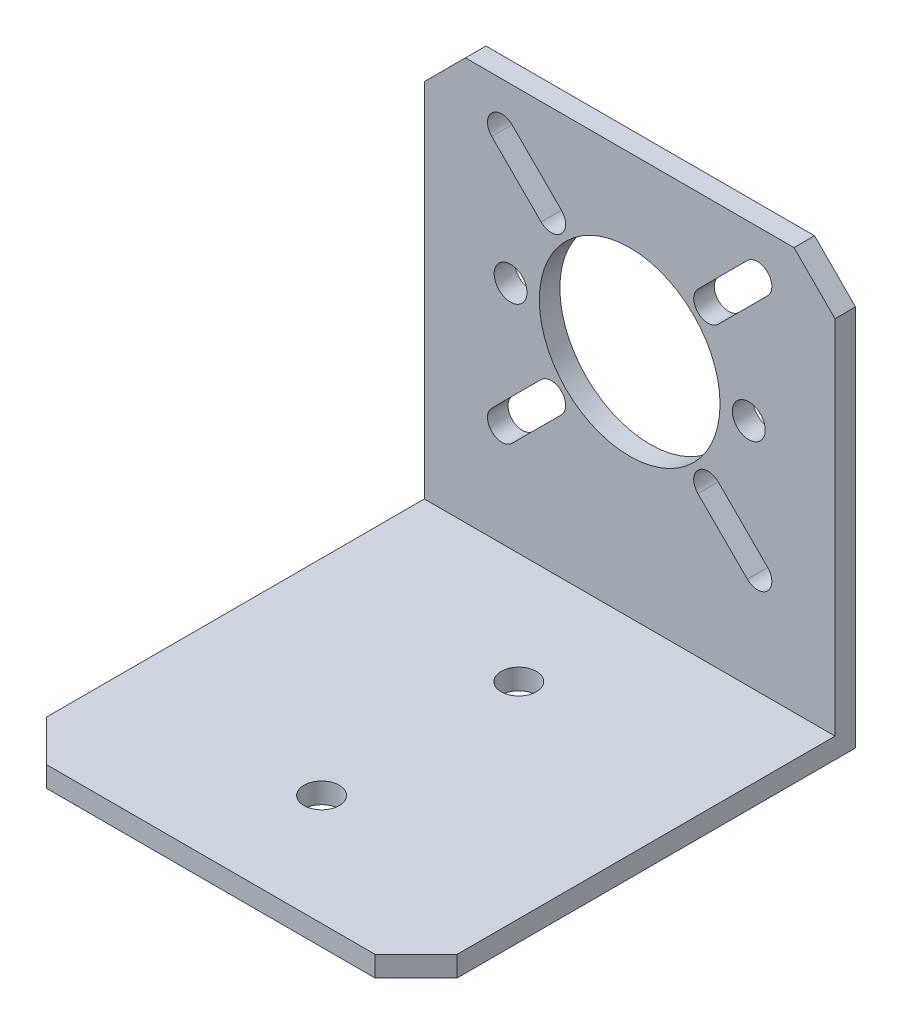
SolidWorks part; units mm, degrees
ref_plane "前视基准面" through (0, 0, 0) normal (0, 0, 1) x (1, 0, 0)
ref_plane "上视基准面" through (0, 0, 0) normal (0, 1, 0) x (1, 0, 0)
ref_plane "右视基准面" through (0, 0, 0) normal (1, 0, 0) x (0, 0, -1)
sketch "草图1" plane through (0, 0, 0) normal (0, 1, 0) x (1, 0, 0)
  line L1 (-25, 1.25) -> (25, 1.25)
  line L2 (-25, 1.25) -> (-25, -1.25)
  line L3 (-25, -1.25) -> (25, -1.25)
  line L4 (25, 1.25) -> (25, -1.25)
  line L5 (-25, 1.25) -> (25, -1.25) construction
  line L6 (-25, -1.25) -> (25, 1.25) construction
  point P1 (0, 0)
  dimension "D1" = 50
  dimension "D2" = 2.5
sketch "草图14" plane through (0, 0, 0) normal (0, 0, 1) x (1, 0, 0)
  line L0 (0, 25.75) -> (0, -25.75) construction
  line L1 (-25, 25.75) -> (25, 25.75)
  line L2 (-25, 25.75) -> (-25, -25.75)
  line L3 (-25, -25.75) -> (25, -25.75)
  line L4 (25, 25.75) -> (25, -25.75)
  line L5 (-25, 25.75) -> (25, -25.75) construction
  line L6 (-25, -25.75) -> (25, 25.75) construction
  line L7 (-22, 4.75) -> (22, 4.75) construction
  line L8 (0, 4.75) -> (-21.3712, 26.1212) construction
  line L9 (-15.5563, 20.3063) -> (-9.5459, 14.2959) construction
  line L10 (-14.3189, 21.5438) -> (-8.3085, 15.5334)
  line L11 (-16.7938, 19.0689) -> (-10.7834, 13.0585)
  line L12 (15.5563, 20.3063) -> (9.5459, 14.2959) construction
  line L13 (14.3189, 21.5438) -> (8.3085, 15.5334)
  line L14 (16.7938, 19.0689) -> (10.7834, 13.0585)
  line L15 (-15.5563, -10.8063) -> (-9.5459, -4.7959) construction
  line L16 (-14.3189, -12.0438) -> (-8.3085, -6.0334)
  line L17 (-16.7938, -9.5689) -> (-10.7834, -3.5585)
  line L18 (15.5563, -10.8063) -> (9.5459, -4.7959) construction
  line L19 (14.3189, -12.0438) -> (8.3085, -6.0334)
  line L20 (16.7938, -9.5689) -> (10.7834, -3.5585)
  circle A0 centre (0, 4.75) radius 11
  circle A1 centre (0, 4.75) radius 13.5 construction
  circle A2 centre (0, 4.75) radius 22 construction
  circle A3 centre (-14.5, 4.75) radius 2
  circle A4 centre (14.5, 4.75) radius 2
  arc A5 (-14.3189, 21.5438) -> (-16.7938, 19.0689) centre (-15.5563, 20.3063) ccw
  arc A6 (-10.7834, 13.0585) -> (-8.3085, 15.5334) centre (-9.5459, 14.2959) ccw
  arc A7 (14.3189, 21.5438) -> (16.7938, 19.0689) centre (15.5563, 20.3063) cw
  arc A8 (10.7834, 13.0585) -> (8.3085, 15.5334) centre (9.5459, 14.2959) cw
  arc A9 (-14.3189, -12.0438) -> (-16.7938, -9.5689) centre (-15.5563, -10.8063) cw
  arc A10 (-10.7834, -3.5585) -> (-8.3085, -6.0334) centre (-9.5459, -4.7959) cw
  arc A11 (14.3189, -12.0438) -> (16.7938, -9.5689) centre (15.5563, -10.8063) ccw
  arc A12 (10.7834, -3.5585) -> (8.3085, -6.0334) centre (9.5459, -4.7959) ccw
  point P0 (0, 0)
  point P21 (-12.5511, 17.3011)
  point P28 (12.5511, 17.3011)
  point P36 (-12.5511, -7.8011)
  point P43 (12.5511, -7.8011)
  dimension "D4" = 22
  dimension "D5" = 27
  dimension "D6" = 44
  dimension "D7" = 4
  dimension "D8" = 29
  dimension "D1" = 51.5
  dimension "D2" = 50
  dimension "D3" = 21
  dimension "D9" = 45
  dimension "D10" = 3.5
extrude "凸台-拉伸1" add sketch "草图14" along normal blind 2.5
sketch "草图16" plane through (0, 0, 2.5) normal (0, 0, 1) x (1, 0, 0)
  line L0 (25, -25.75) -> (25, 25.75) construction
  line L1 (-25, -25.75) -> (25, -25.75)
  line L2 (-25, -25.75) -> (-25, -23.25)
  line L3 (-25, -23.25) -> (25, -23.25)
  line L4 (25, -25.75) -> (25, -23.25)
  dimension "D1" = 2.5
extrude "凸台-拉伸2" add sketch "草图16" along normal offset from surface (51 mm away) 53.5 up to face at (-12.5511, -7.8011, 0)
sketch "草图17" plane through (0, -23.25, 0) normal (0, 1, 0) x (1, 0, 0)
  line L0 (0, -2.5) -> (0, -53.5) construction
  line L1 (25, -2.5) -> (-25, -2.5) construction
  line L2 (25, -53.5) -> (-25, -53.5) construction
  circle A6 centre (0, -40) radius 2.15
  circle A7 centre (0, -16) radius 2.15
  point P14 (0, -28)
  dimension "D1" = 12
  dimension "D2" = 12
extrude "切除-拉伸1" cut sketch "草图17" against normal through all
chamfer "倒角1" distance 5 angle 45 4 edges at (-25, 25.75, 1.25) (25, 25.75, 1.25) (-25, -24.5, 53.5) (25, -24.5, 53.5)
sketch "折弯-线1" plane through (0, 0, 0) normal (0, 1, 0) x (1, 0, 0)
sketch "边界框1" plane through (0, 0, 0) normal (0, 1, 0) x (1, 0, 0)
